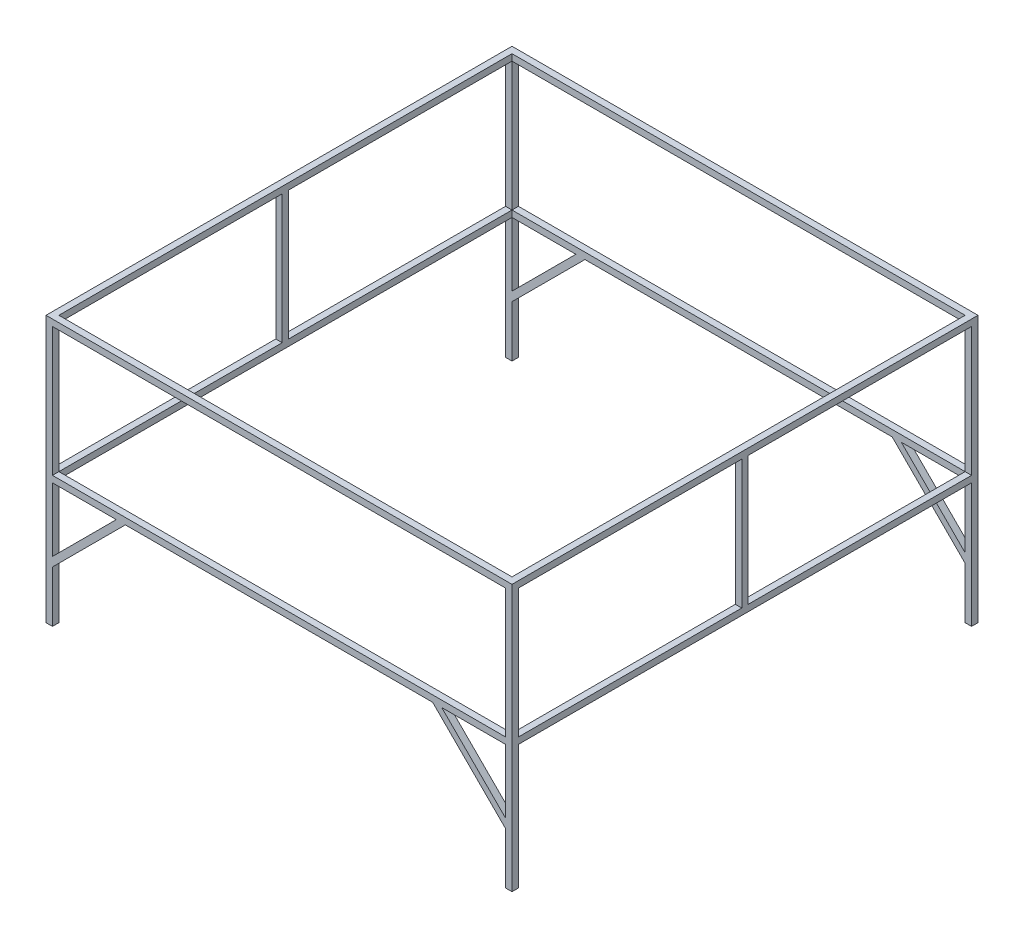
SolidWorks part; units mm, degrees
ref_plane "Front Plane" through (0, 0, 0) normal (0, 0, 1) x (1, 0, 0)
ref_plane "Top Plane" through (0, 0, 0) normal (0, 1, 0) x (1, 0, 0)
ref_plane "Right Plane" through (0, 0, 0) normal (1, 0, 0) x (0, 0, -1)
sketch "Sketch1" plane through (0, 0, 0) normal (0, 1, 0) x (1, 0, 0)
  line L0 (-559.125, 559.125) -> (-559.125, -559.125)
  line L1 (-575, 575) -> (575, 575)
  line L2 (-575, 575) -> (-575, -575)
  line L3 (-575, -575) -> (575, -575)
  line L4 (575, 575) -> (575, -575)
  line L5 (-575, 575) -> (575, -575) construction
  line L6 (-575, -575) -> (575, 575) construction
  line L7 (-559.125, -559.125) -> (559.125, -559.125)
  line L8 (559.125, 559.125) -> (559.125, -559.125)
  line L9 (-559.125, 559.125) -> (559.125, 559.125)
  point P0 (0, 0)
  dimension "D1" = 1150
  dimension "D2" = 1150
  dimension "D3" = 15.875
extrude "Boss-Extrude1" add sketch "Sketch1" along normal blind 15.875
sketch "Sketch2" plane through (0, 15.875, 0) normal (0, 1, 0) x (1, 0, 0)
  line L0 (-559.125, 559.125) -> (-559.125, -559.125) construction
  line L1 (-575, 575) -> (-559.125, 575)
  line L2 (-575, 575) -> (-575, 559.125)
  line L3 (-575, 559.125) -> (-559.125, 559.125)
  line L4 (-559.125, 575) -> (-559.125, 559.125)
  line L5 (559.125, 559.125) -> (-559.125, 559.125) construction
  line L6 (-575, 575) -> (-575, -575) construction
  line L7 (-575, -575) -> (-559.125, -575)
  line L8 (-575, -575) -> (-575, -559.125)
  line L9 (-575, -559.125) -> (-559.125, -559.125)
  line L10 (-559.125, -575) -> (-559.125, -559.125)
  line L11 (-575, 7.9375) -> (-559.125, 7.9375)
  line L12 (-575, 7.9375) -> (-575, -7.9375)
  line L13 (-575, -7.9375) -> (-559.125, -7.9375)
  line L14 (-559.125, 7.9375) -> (-559.125, -7.9375)
  point P21 (-575, 0)
  dimension "D1" = 15.875
extrude "Boss-Extrude2" add sketch "Sketch2" along normal blind 318.25
sketch "Sketch3" plane through (0, 334.125, 0) normal (0, 1, 0) x (1, 0, 0)
  line L4 (575, 575) -> (-575, 575)
  line L5 (575, -575) -> (575, 575)
  line L6 (-575, -575) -> (575, -575)
  line L7 (-575, 575) -> (-575, -575)
  line L8 (575, 575) -> (-575, 575)
  line L9 (575, -575) -> (575, 575)
  line L10 (-575, -575) -> (575, -575)
  line L11 (-575, 575) -> (-575, -575)
  line L12 (-559.125, 559.125) -> (-559.125, -559.125)
  line L13 (-559.125, -559.125) -> (559.125, -559.125)
  line L14 (559.125, -559.125) -> (559.125, 559.125)
  line L15 (559.125, 559.125) -> (-559.125, 559.125)
  line L16 (-559.125, 559.125) -> (-559.125, -559.125)
  line L17 (-559.125, -559.125) -> (559.125, -559.125)
  line L18 (559.125, -559.125) -> (559.125, 559.125)
  line L19 (559.125, 559.125) -> (-559.125, 559.125)
  dimension "D1" = 0
  dimension "D2" = 0
extrude "Boss-Extrude3" add sketch "Sketch3" along normal blind 15.875
mirror "Mirror1" about plane through (0, 0, 0) normal (1, 0, 0) of "Boss-Extrude2"
sketch "Sketch4" plane through (0, 0, 575) normal (0, 0, 1) x (1, 0, 0)
  line L0 (379.125, 0) -> (559.125, -180)
  line L1 (575, 0) -> (559.125, 0)
  line L2 (575, 0) -> (575, -307)
  line L3 (575, -307) -> (559.125, -307)
  line L4 (559.125, 0) -> (559.125, -307)
  line L5 (379.125, 0) -> (390.3503, 11.2253)
  line L6 (559.125, -180) -> (570.3503, -168.7747)
  line L7 (390.3503, 11.2253) -> (570.3503, -168.7747)
  line L8 (-575, 0) -> (575, 0) construction
  point P11 (0, 0)
  point P12 (0, 0)
  point P13 (0, 0)
  line M11 (-575, 0) -> (575, 0)
  dimension "D1" = 307
  dimension "D2" = 15.875
  dimension "D3" = 15.875
  dimension "D4" = 180
  dimension "D5" = 45
extrude "Boss-Extrude4" add sketch "Sketch4" against normal blind 15.875 contours L4 L7 L6 L3 L2 M11
mirror "Mirror2" about plane through (0, 0, 0) normal (1, 0, 0) of "Boss-Extrude4" second plane through (0, 0, 0) second plane normal (0, 0, 1)
